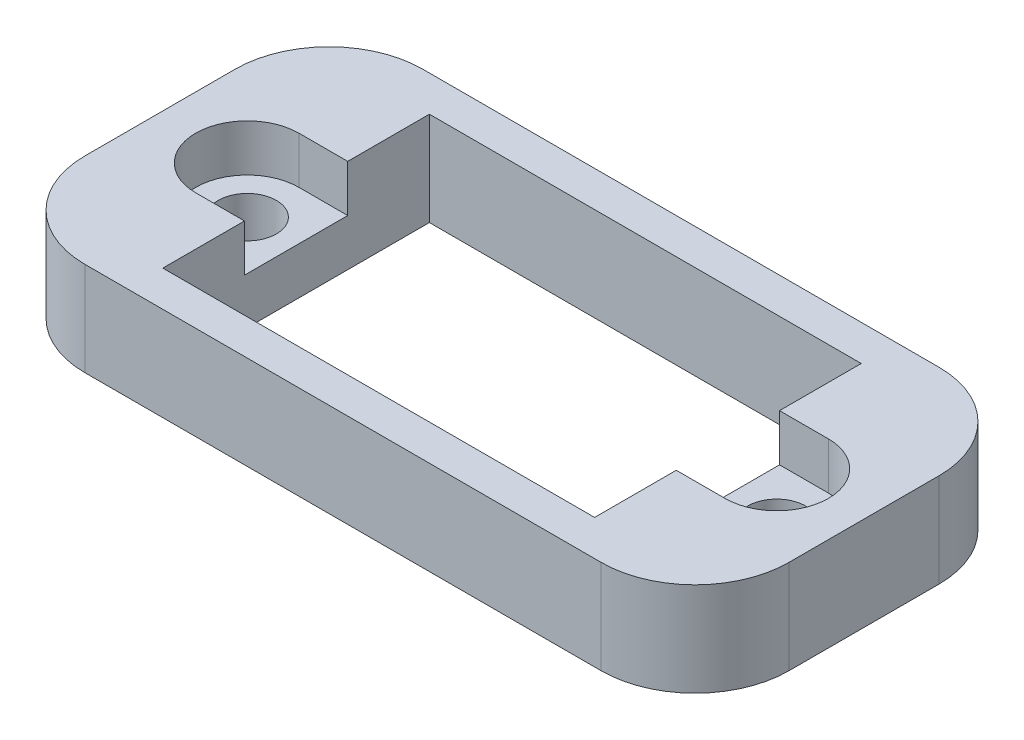
SolidWorks part; units mm, degrees
ref_plane "Front Plane" through (0, 0, 0) normal (0, 0, 1) x (1, 0, 0)
ref_plane "Top Plane" through (0, 0, 0) normal (0, 1, 0) x (1, 0, 0)
ref_plane "Right Plane" through (0, 0, 0) normal (1, 0, 0) x (0, 0, -1)
sketch "Sketch1" plane through (0, 0, 0) normal (0, 1, 0) x (1, 0, 0)
  line L0 (-1000, 0) -> (49000, 0) construction
  line L1 (-18.75, -9) -> (18.75, -9)
  line L2 (-18.75, -9) -> (-18.75, 9)
  line L3 (-18.75, 9) -> (18.75, 9)
  line L4 (18.75, -9) -> (18.75, 9)
  line L5 (-18.75, -9) -> (18.75, 9) construction
  line L6 (-18.75, 9) -> (18.75, -9) construction
  line L7 (-11.5, -7.1) -> (11.5, -7.1)
  line L8 (-11.5, -7.1) -> (-11.5, 7.1)
  line L9 (-11.5, 7.1) -> (11.5, 7.1)
  line L10 (11.5, -7.1) -> (11.5, 7.1)
  line L11 (-11.5, -7.1) -> (11.5, 7.1) construction
  line L12 (-11.5, 7.1) -> (11.5, -7.1) construction
  line L13 (-14.1, -997.45) -> (-14.1, 49002.55) construction
  line L14 (14.1, -997.45) -> (14.1, 49002.55) construction
  circle A0 centre (-14.1, 0) radius 1.55
  circle A1 centre (14.1, 0) radius 1.55
  point P0 (0, 0)
  point P6 (0, 0)
  dimension "D8" = 3.1
  dimension "D10" = 3.1
  dimension "D1" = 37.5
  dimension "D2" = 18
  dimension "D3" = 23
  dimension "D4" = 14.2
  dimension "D5" = 2.6
  dimension "D6" = 2.6
  dimension "D7" = 0
  dimension "D9" = 0
extrude "Boss-Extrude1" add sketch "Sketch1" along normal blind 5
sketch "Sketch2" plane through (0, 5, 0) normal (0, 1, 0) x (1, 0, 0)
  line L0 (-14.1, 2.75) -> (-11.5, 2.75)
  line L1 (-11.5, 7.1) -> (-11.5, -7.1) construction
  line L2 (-14.1, -2.75) -> (-11.5, -2.75)
  line L3 (14.1, 2.75) -> (11.5, 2.75)
  line L12 (14.1, -2.75) -> (11.5, -2.75)
  circle A0 centre (-14.1, 0) radius 2.75
  circle A1 centre (14.1, 0) radius 2.75
  line M5 (11.5, 7.1) -> (11.5, -7.1)
  line M7 (-11.5, -7.1) -> (-11.5, 7.1)
  circle M9 centre (-14.1, 0) radius 1.55
  circle M10 centre (14.1, 0) radius 1.55
  dimension "D1" = 5.5
  dimension "D2" = 5.5
  dimension "D3" = 2.6
  dimension "D4" = 2.6
  dimension "D5" = 2.75
  dimension "D6" = 2.75
extrude "Cut-Extrude1" cut sketch "Sketch2" against normal blind 2.5 contours A1 L3 M5 | A1 L12 M5 | A1 M5 M10 | A0 L2 M7 | A0 L0 M7 | A0 M7 M9
fillet "Fillet1" radius 5 4 edges at (-18.75, 2.5, -9) (-18.75, 2.5, 9) (18.75, 2.5, -9) (18.75, 2.5, 9)
